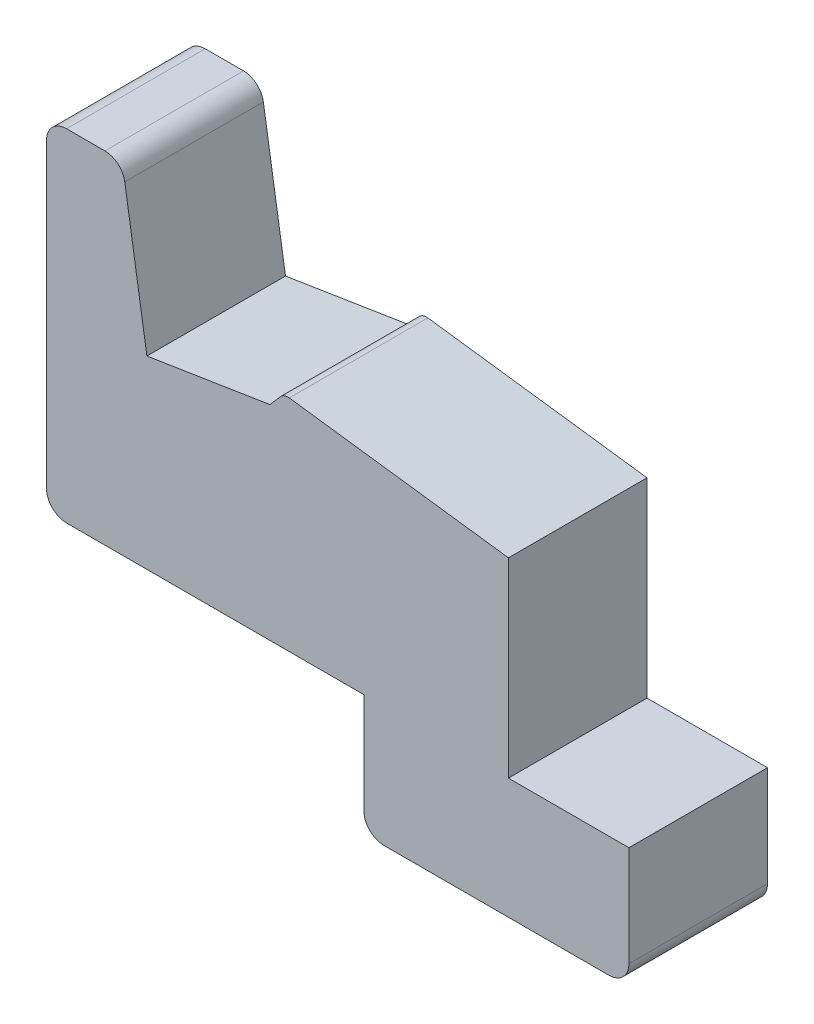
SolidWorks part; units mm, degrees
ref_plane "Front Plane" through (0, 0, 0) normal (0, 0, 1) x (1, 0, 0)
ref_plane "Top Plane" through (0, 0, 0) normal (0, 1, 0) x (1, 0, 0)
ref_plane "Right Plane" through (0, 0, 0) normal (1, 0, 0) x (0, 0, -1)
sketch "Sketch1" plane through (0, 0, 0) normal (0, 0, 1) x (1, 0, 0)
  line L1 (11.5, 8.5) -> (-11.5, 8.5)
  line L2 (11.5, 8.5) -> (11.5, -8.5)
  line L3 (11.5, -8.5) -> (-11.5, -8.5)
  line L4 (-11.5, 8.5) -> (-11.5, -8.5)
  line L5 (11.5, 8.5) -> (-11.5, -8.5) construction
  line L6 (11.5, -8.5) -> (-11.5, 8.5) construction
  point P0 (0, 0)
  dimension "D1" = 23
  dimension "D2" = 17
extrude "Boss-Extrude1" add sketch "Sketch1" along normal blind 6.9
sketch "Sketch2" plane through (0, 0, 6.9) normal (0, 0, 1) x (1, 0, 0)
  line L0 (-11.5, -8.5) -> (11.5, -8.5) construction
  line L1 (17.5, -8.5) -> (4.3, -8.5)
  line L2 (17.5, -8.5) -> (17.5, -14.5)
  line L3 (17.5, -14.5) -> (4.3, -14.5)
  line L4 (4.3, -8.5) -> (4.3, -14.5)
  line L6 (11.5, -8.5) -> (11.5, 8.5) construction
  dimension "D1" = 13.2
  dimension "D2" = 6
  dimension "D3" = 6
extrude "Boss-Extrude2" add sketch "Sketch2" against normal up to surface (6.9 mm away) up to face at (0, 0, 0)
sketch "Sketch3" plane through (0, 0, 6.9) normal (0, 0, 1) x (1, 0, 0)
  line L0 (11.5, 1) -> (0.3219, 2.4732)
  line L2 (0.3219, 2.4732) -> (-0.3763, 1.6699)
  line L3 (-0.3763, 1.6699) -> (-6.5, 0.7)
  line L4 (-6.5, 0.7) -> (-7.8786, 9.4044)
  line L7 (-11.5, -8.5) -> (4.3, -8.5) construction
  line L8 (11.5, -8.5) -> (11.5, 8.5) construction
  dimension "D1" = 9
  dimension "D2" = 9.5
  dimension "D3" = 18
  dimension "D4" = 6.2
  dimension "D5" = 1.0643
  dimension "D6" = 40
  dimension "D7" = 9.2
extrude "Cut-Extrude1" cut sketch "Sketch3" against normal through all and the other way through all flip side to cut
fillet "Fillet1" radius 0.5 1 edges at (0.3219, 2.4732, 3.45)
fillet "Fillet2" radius 1 5 edges at (17.5, -14.5, 3.45) (4.3, -14.5, 3.45) (-11.5, -8.5, 3.45) (-7.7354, 8.5, 3.45) (-11.5, 8.5, 3.45)
sketch "Sketch5" plane through (0, 0, 0) normal (0, 0, 1) x (1, 0, 0)
  text T0 "SeeMeCNC\r\n87915  R1" font "1CamBam_Stick_9" height 1.8
